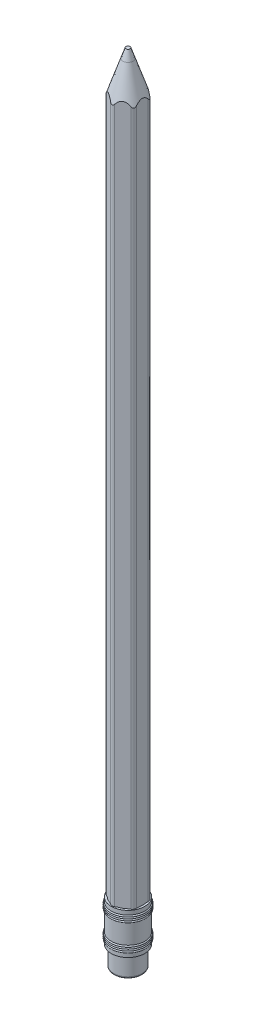
SolidWorks part; units mm, degrees
other "Case"
other "Lead"
ref_plane "Front Plane" through (0, 0, 0) normal (0, 0, 1) x (1, 0, 0)
ref_plane "Top Plane" through (0, 0, 0) normal (0, 1, 0) x (1, 0, 0)
ref_plane "Right Plane" through (0, 0, 0) normal (1, 0, 0) x (0, 0, -1)
sketch "Sketch1" plane through (0, 0, 0) normal (0, 1, 0) x (1, 0, 0)
  circle A0 centre (0, 0) radius 1.25
  dimension "D1" = 2.5
extrude "Lead" add sketch "Sketch1" along normal blind 185
sketch "Sketch2" plane through (0, 0, 0) normal (0, -1, 0) x (1, 0, 0)
  line L1 (-3.5, -2.0207) -> (0, -4.0415)
  line L2 (0, -4.0415) -> (3.5, -2.0207)
  line L3 (3.5, -2.0207) -> (3.5, 2.0207)
  line L4 (3.5, 2.0207) -> (0, 4.0415)
  line L5 (0, 4.0415) -> (-3.5, 2.0207)
  line L6 (-3.5, 2.0207) -> (-3.5, -2.0207)
  circle A0 centre (0, 0) radius 3.5 construction
  circle A2 centre (0, 0) radius 1.25
  circle A3 centre (0, 0) radius 1.25 construction
  dimension "D1" = 7
  dimension "D2" = 7
extrude "Case" add sketch "Sketch2" against normal up to surface (185 mm away) separate body up to face at (0, 185, 1.25)
sketch "Sketch4" plane through (0, 0, 0) normal (0, -1, 0) x (1, 0, 0)
  circle A0 centre (0, 0) radius 3.5
  dimension "D1" = 7
extrude "Boss-Extrude5" add sketch "Sketch4" along normal blind 10 separate body
fillet "Fillet4" radius 0.5 1 edges at (0, -10, -3.5)
sketch "Sketch6" plane through (0, 0, 0) normal (0, 0, 1) x (1, 0, 0)
  line L0 (0, 0) -> (-3.5, 0) construction
  line L1 (-3.6, 5) -> (-4.1, 5)
  line L2 (-3.6, 5) -> (-3.6, -5) construction
  line L3 (-3.6, -5) -> (-4.1, -5)
  line L4 (-4.1, 5) -> (-4.1, -5) construction
  line L5 (-4.1, -5) -> (-4.1, -4)
  line L6 (-4.1, -2.4) -> (-4.1, 2.4)
  line L7 (-4.1, 4) -> (-4.1, 5)
  line L8 (-3.85, -5) -> (-3.85, 5) construction
  line L9 (-3.6, -5) -> (-3.6, -4)
  line L10 (-3.6, -2.4) -> (-3.6, 2.4)
  line L11 (-3.6, 4) -> (-3.6, 5)
  line L12 (0, -10) -> (0, 0) construction
  line L13 (-3, -10) -> (3, -10) construction
  arc A0 (-4.1, 4) -> (-4.1, 3.6) centre (-4.1, 3.8) ccw
  arc A1 (-4.1, 3.6) -> (-4.1, 3.2) centre (-4.1, 3.4) ccw
  arc A2 (-4.1, 3.2) -> (-4.1, 2.8) centre (-4.1, 3) ccw
  arc A3 (-4.1, 2.8) -> (-4.1, 2.4) centre (-4.1, 2.6) ccw
  arc A4 (-4.1, -2.8) -> (-4.1, -2.4) centre (-4.1, -2.6) cw
  arc A5 (-4.1, -3.2) -> (-4.1, -2.8) centre (-4.1, -3) cw
  arc A6 (-4.1, -3.6) -> (-4.1, -3.2) centre (-4.1, -3.4) cw
  arc A7 (-4.1, -4) -> (-4.1, -3.6) centre (-4.1, -3.8) cw
  arc A8 (-3.6, -4) -> (-3.6, -3.6) centre (-3.6, -3.8) ccw
  arc A9 (-3.6, -3.6) -> (-3.6, -3.2) centre (-3.6, -3.4) ccw
  arc A10 (-3.6, -3.2) -> (-3.6, -2.8) centre (-3.6, -3) ccw
  arc A11 (-3.6, -2.8) -> (-3.6, -2.4) centre (-3.6, -2.6) ccw
  arc A12 (-3.6, 2.8) -> (-3.6, 2.4) centre (-3.6, 2.6) cw
  arc A13 (-3.6, 3.2) -> (-3.6, 2.8) centre (-3.6, 3) cw
  arc A14 (-3.6, 3.6) -> (-3.6, 3.2) centre (-3.6, 3.4) cw
  arc A15 (-3.6, 4) -> (-3.6, 3.6) centre (-3.6, 3.8) cw
  point P4 (-3.6, 0)
  dimension "D5" = 0.4
  dimension "D1" = 10
  dimension "D2" = 0.5
  dimension "D3" = 4.1
  dimension "D4" = 1
  dimension "D6" = 4
revolve "Revolve1" add sketch "Sketch6" angle 360 about L12
fillet "Fillet5" radius 1 6 edges at (0, 92.5, -4.0415) (3.5, 92.5, -2.0207) (3.5, 92.5, 2.0207) (0, 92.5, 4.0415) (-3.5, 92.5, 2.0207) (-3.5, 92.5, -2.0207)
sketch "Sketch9" plane through (0, 0, 0) normal (0, 0, 1) x (1, 0, 0)
  line L0 (0, 185) -> (0, 170) construction
  line L1 (1.25, 185) -> (-1.25, 185) construction
  line L2 (-0.5, 185) -> (-5.5, 170)
  line L3 (-5.5, 170) -> (-5.5, 185)
  line L4 (-5.5, 185) -> (-0.5, 185)
  dimension "D1" = 15
  dimension "D2" = 0.5
  dimension "D3" = 5
  dimension "D4" = 15
revolve "Cut-Revolve1" cut sketch "Sketch9" angle 360 about L0
